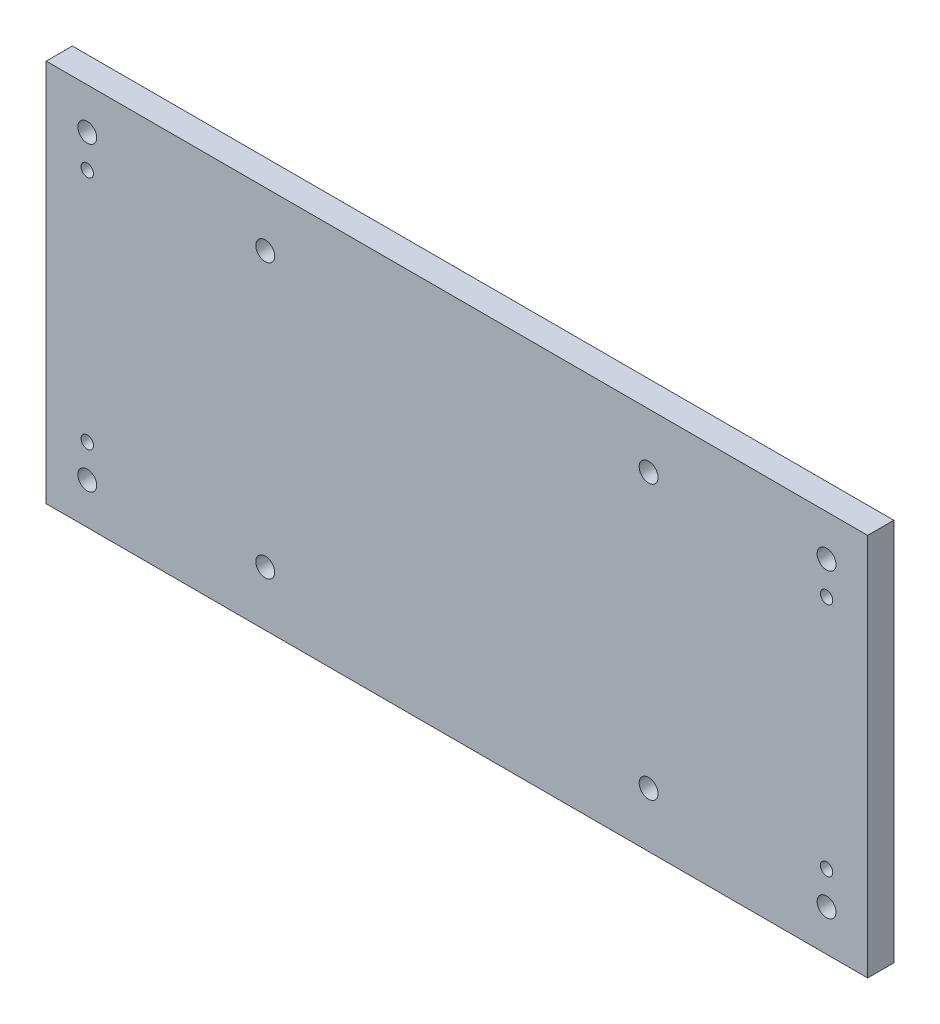
SolidWorks part; units mm, degrees
ref_plane "Front Plane" through (0, 0, 0) normal (0, 0, 1) x (1, 0, 0)
ref_plane "Top Plane" through (0, 0, 0) normal (0, 1, 0) x (1, 0, 0)
ref_plane "Right Plane" through (0, 0, 0) normal (1, 0, 0) x (0, 0, -1)
sketch "Sketch1" plane through (0, 0, 0) normal (0, 0, 1) x (1, 0, 0)
  line L1 (0, 0) -> (150, 0)
  line L2 (0, 0) -> (0, -70)
  line L3 (0, -70) -> (150, -70)
  line L4 (150, 0) -> (150, -70)
  line L5 (7.5, -7.5) -> (142.5, -7.5) construction
  line L6 (7.5, -7.5) -> (7.5, -62.5) construction
  line L7 (7.5, -62.5) -> (142.5, -62.5) construction
  line L8 (142.5, -7.5) -> (142.5, -62.5) construction
  line L9 (7.5, -13.5) -> (142.5, -13.5) construction
  line L10 (7.5, -13.5) -> (7.5, -56.5) construction
  line L11 (7.5, -56.5) -> (142.5, -56.5) construction
  line L12 (142.5, -13.5) -> (142.5, -56.5) construction
  line L13 (40, -10) -> (110, -10) construction
  line L14 (40, -10) -> (40, -60) construction
  line L15 (40, -60) -> (110, -60) construction
  line L16 (110, -10) -> (110, -60) construction
  circle A0 centre (7.5, -7.5) radius 1.725
  circle A1 centre (142.5, -7.5) radius 1.725
  circle A2 centre (142.5, -62.5) radius 1.725
  circle A3 centre (7.5, -62.5) radius 1.725
  circle A4 centre (7.5, -13.5) radius 1.13
  circle A5 centre (142.5, -13.5) radius 1.13
  circle A6 centre (142.5, -56.5) radius 1.13
  circle A7 centre (7.5, -56.5) radius 1.13
  circle A8 centre (40, -10) radius 1.725
  circle A9 centre (40, -60) radius 1.725
  circle A10 centre (110, -10) radius 1.725
  circle A11 centre (110, -60) radius 1.725
  dimension "D1" = 3.45
  dimension "D12" = 2.26
  dimension "D2" = 135
  dimension "D3" = 55
  dimension "D4" = 150
  dimension "D5" = 7.5
  dimension "D6" = 43
  dimension "D7" = 6
  dimension "D8" = 70
  dimension "D9" = 7.5
  dimension "D10" = 50
  dimension "D11" = 10
  dimension "D13" = 70
  dimension "D14" = 40
extrude "Boss-Extrude1" add sketch "Sketch1" along normal blind 4.7752 contours L4 L1 L2 L3 A7 L10 A4 L9 A5 L12 A6 L11 A3 A2 A1 A0
hole_wizard "#4-40 Tapped Hole1" positions "3DSketch1" profile "Sketch2" tap size "#4-40" standard "ANSI Inch" end condition through all
sketch3d "3DSketch1"
  circle A0 centre (142.5, -13.5, 4.7752) radius 1.13 construction
  circle A1 centre (142.5, -56.5, 4.7752) radius 1.13 construction
  circle A2 centre (7.5, -56.5, 4.7752) radius 1.13 construction
  circle A3 centre (7.5, -13.5, 4.7752) radius 1.13 construction
  point P0 (7.5, -13.5, 4.7752)
  point P2 (7.5, -56.5, 4.7752)
  point P4 (142.5, -56.5, 4.7752)
  point P6 (142.5, -13.5, 4.7752)
  point P11 (142.5, -13.5, 5.9052)
  point P14 (142.5, -56.5, 5.9052)
  point P15 (0, 0, 0)
  point P18 (7.5, -56.5, 5.9052)
  point P21 (7.5, -13.5, 5.9052)
sketch "Sketch2" plane through (7.5, -13.5, 4.7752) normal (1, 0, 0) x (0, -1, 0)
  line L0 (0, 0) -> (0, 4.7752)
  line L1 (0, 4.7752) -> (1.1303, 4.7752)
  line L2 (1.1303, 4.7752) -> (1.1303, 0)
  line L5 (1.1303, 0) -> (0, 0)
  line L11 (0, -6.35) -> (0, 107.95) construction
  dimension "Thru Tap Drill Dia." = 2.2606
  dimension "Thru Tap Drill Depth" = 4.7752
cosmetic thread "Hole Thread1"
cosmetic thread "Hole Thread2"
cosmetic thread "Hole Thread3"
cosmetic thread "Hole Thread4"
equation "\"D5@Sketch1\"=(\"D4@Sketch1\"-\"D2@Sketch1\")/2"
equation "\"D9@Sketch1\"= (\"D8@Sketch1\"-\"D3@Sketch1\")/2"
equation "\"D11@Sketch1\"=(\"D8@Sketch1\"-\"D10@Sketch1\")/2"
equation "\"D14@Sketch1\"=(\"D4@Sketch1\"-\"D13@Sketch1\")/2"
